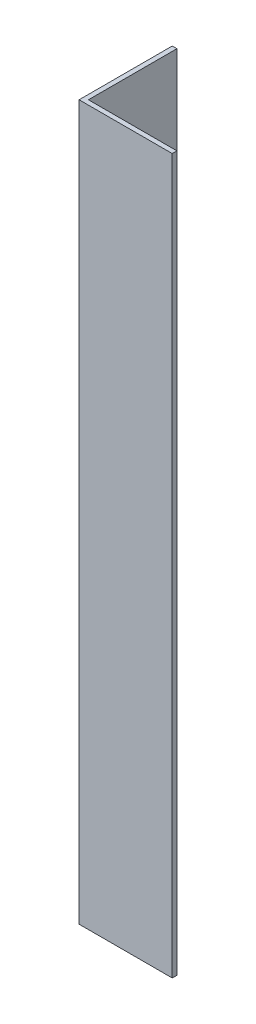
SolidWorks part; units mm, degrees
material "1060 Сплав"
ref_plane "Спереди" through (0, 0, 0) normal (0, 0, 1) x (1, 0, 0)
ref_plane "Сверху" through (0, 0, 0) normal (0, 1, 0) x (1, 0, 0)
ref_plane "Справа" through (0, 0, 0) normal (1, 0, 0) x (0, 0, -1)
sketch "Эскиз1" plane through (0, 0, 0) normal (0, 1, 0) x (1, 0, 0)
  line L0 (0, 0) -> (0, 15)
  line L1 (0, 15) -> (0.75, 15)
  line L2 (0.75, 15) -> (0.75, 0.75)
  line L3 (0.75, 0.75) -> (15, 0.75)
  line L4 (15, 0.75) -> (15, 0)
  line L5 (15, 0) -> (0, 0)
  dimension "D1" = 0.75
  dimension "D2" = 15
extrude "Бобышка-Вытянуть1" add sketch "Эскиз1" along normal blind 115
sketch "Эскиз2" plane through (0, 0, 0) normal (0, 0, 1) x (1, 0, 0)
  line L0 (7.5, 115) -> (7.5, 0) construction
  line L1 (0, 115) -> (15, 115) construction
  line L2 (0, 0) -> (15, 0) construction
